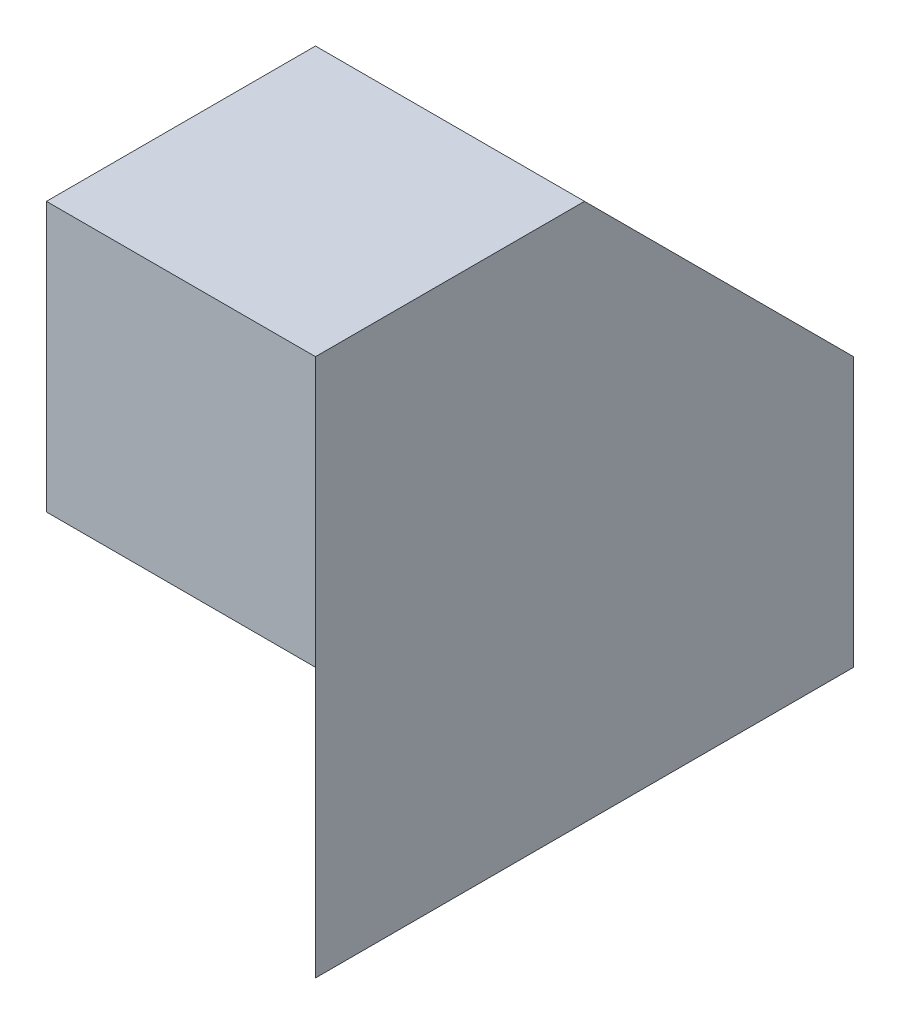
SolidWorks part; units mm, degrees
ref_plane "Front Plane" through (0, 0, 0) normal (0, 0, 1) x (1, 0, 0)
ref_plane "Top Plane" through (0, 0, 0) normal (0, 1, 0) x (1, 0, 0)
ref_plane "Right Plane" through (0, 0, 0) normal (1, 0, 0) x (0, 0, -1)
sketch "Sketch1" plane through (0, 0, 0) normal (0, 0, 1) x (1, 0, 0)
  line L1 (0, 0) -> (40, 0)
  line L2 (0, 0) -> (0, 20)
  line L3 (0, 20) -> (40, 20)
  line L4 (40, 0) -> (40, 20)
  dimension "D1" = 20
  dimension "D2" = 40
extrude "Boss-Extrude1" add sketch "Sketch1" along normal blind 40
sketch "Sketch2" plane through (0, 20, 0) normal (0, 1, 0) x (1, 0, 0)
  line L0 (0, 0) -> (40, -40)
  line L1 (40, -40) -> (0, -40)
  line L2 (0, -40) -> (0, 0)
extrude "Cut-Extrude1" cut sketch "Sketch2" against normal blind 40
sketch "Sketch3" plane through (40, 0, 0) normal (1, 0, 0) x (0, 0, -1)
  line L1 (-40, 20) -> (0, 20)
  line L2 (-40, 20) -> (-40, 40)
  line L3 (-40, 40) -> (0, 40)
  line L4 (0, 20) -> (0, 40)
  dimension "D1" = 40
  dimension "D2" = 20
extrude "Boss-Extrude2" add sketch "Sketch3" against normal blind 20
sketch "Sketch4" plane through (20, 0, 0) normal (-1, 0, 0) x (0, 0, 1)
  line L0 (0, 20) -> (20, 40)
  line L1 (0, 40) -> (40, 40) construction
  line L2 (20, 40) -> (0, 40)
  line L3 (0, 40) -> (0, 20)
extrude "Cut-Extrude2" cut sketch "Sketch4" against normal blind 20
